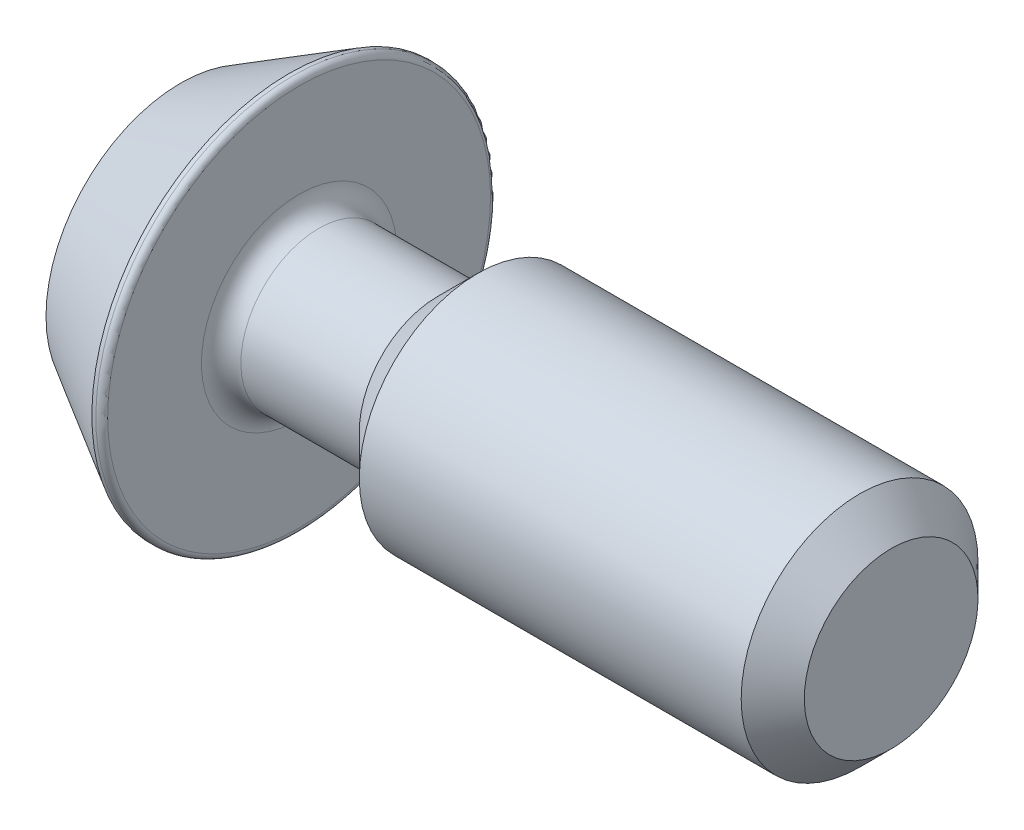
SolidWorks part; units mm, degrees
ref_plane "Спереди" through (0, 0, 0) normal (0, 0, 1) x (1, 0, 0)
ref_plane "Сверху" through (0, 0, 0) normal (0, 1, 0) x (1, 0, 0)
ref_plane "Справа" through (0, 0, 0) normal (1, 0, 0) x (0, 0, -1)
sketch "Эскиз1" plane through (0, 0, 0) normal (0, 0, 1) x (1, 0, 0)
  line L0 (0, 0) -> (0, 6.8246)
  line L1 (5.5, 10) -> (6, 10)
  line L2 (6, 10) -> (6, 3.95)
  line L4 (36, 6) -> (36, 0)
  line L5 (36, 0) -> (0, 0) construction
  line L6 (0, 0) -> (36, 0)
  line L7 (0, 6.8246) -> (5.5, 10)
  line L8 (6, 3.95) -> (13, 3.95)
  line L9 (13, 3.95) -> (15.05, 6)
  line L10 (15.05, 6) -> (36, 6)
  line L11 (0, 0) -> (-6.2497, 0) construction
  dimension "D4" = 36
  dimension "D1" = 0.5
  dimension "D2" = 12
  dimension "D3" = 20
  dimension "D5" = 6
  dimension "D6" = 30
  dimension "D7" = 7
  dimension "D8" = 45
  dimension "D9" = 7.9
revolve "Повернуть1" add sketch "Эскиз1" angle 360 about L5
cosmetic thread "Условное изображение резьбы1" parameters "D2"=10.072
sketch "Эскиз2" plane through (0, 0, 0) normal (-1, 0, 0) x (0, 0, 1)
  line L1 (1.7321, 3) -> (-1.7321, 3)
  line L2 (-1.7321, 3) -> (-3.4641, 0)
  line L3 (-3.4641, 0) -> (-1.7321, -3)
  line L4 (-1.7321, -3) -> (1.7321, -3)
  line L5 (1.7321, -3) -> (3.4641, 0)
  line L6 (3.4641, 0) -> (1.7321, 3)
  circle A0 centre (0, 0) radius 3 construction
  dimension "D1" = 6
extrude "Вырез-Вытянуть1" cut sketch "Эскиз2" against normal blind 4
fillet "Скругление1" radius 0.3 1 edges at (6, 10, 0)
chamfer "Фаска1" distance 1.6 angle 45 1 edges at (36, 6, 0)
fillet "Скругление2" radius 1 1 edges at (6, 3.95, 0)
